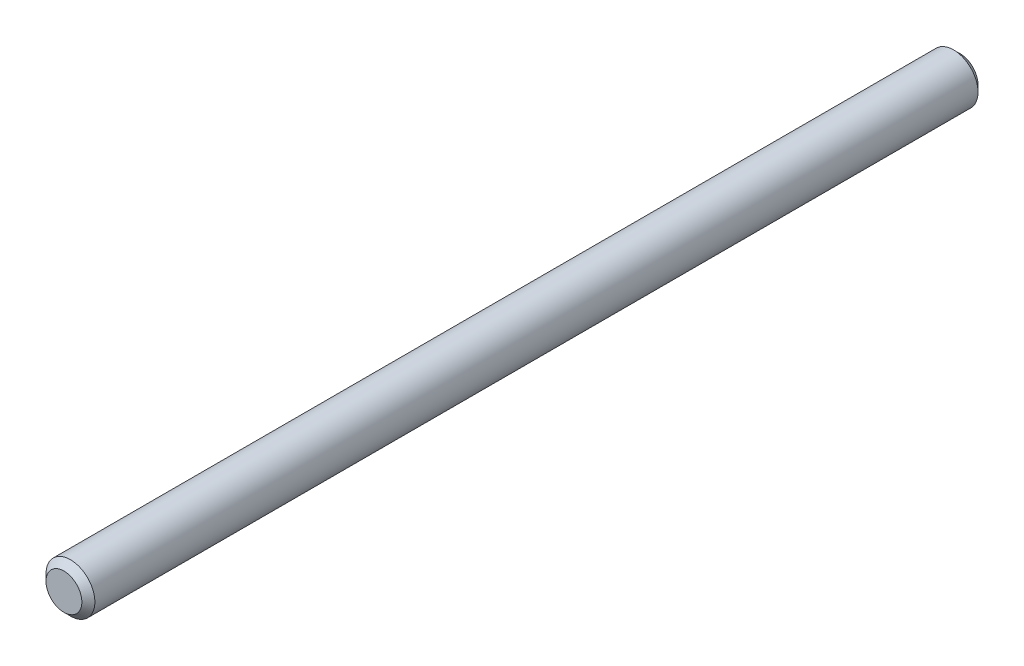
SolidWorks part; units mm, degrees
ref_plane "Front Plane" through (0, 0, 0) normal (0, 0, 1) x (1, 0, 0)
ref_plane "Top Plane" through (0, 0, 0) normal (0, 1, 0) x (1, 0, 0)
ref_plane "Right Plane" through (0, 0, 0) normal (1, 0, 0) x (0, 0, -1)
sketch "Sketch1" plane through (0, 0, 0) normal (0, 0, 1) x (1, 0, 0)
  circle A0 centre (0, 0) radius 7.5
  dimension "D1" = 15
extrude "Boss-Extrude1" add sketch "Sketch1" along normal mid plane 275
chamfer "Chamfer1" distance 2 angle 45 2 edges at (7.5, 0, 137.5) (7.5, 0, -137.5)
